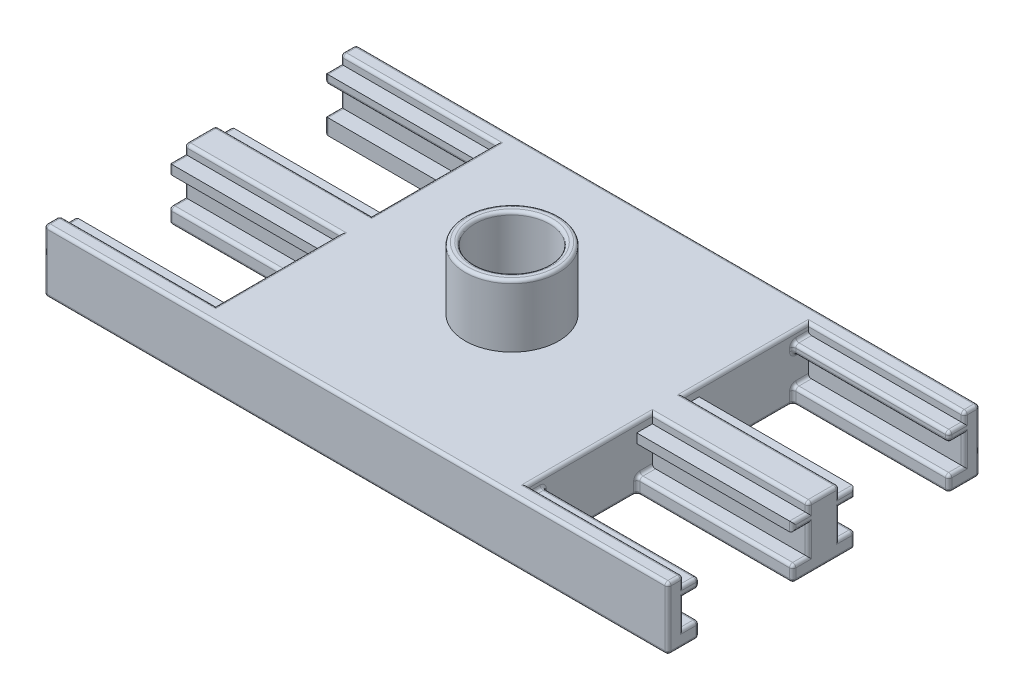
SolidWorks part; units mm, degrees
ref_plane "Front Plane" through (0, 0, 0) normal (0, 0, 1) x (1, 0, 0)
ref_plane "Top Plane" through (0, 0, 0) normal (0, 1, 0) x (1, 0, 0)
ref_plane "Right Plane" through (0, 0, 0) normal (1, 0, 0) x (0, 0, -1)
sketch "Sketch1" plane through (0, 0, 0) normal (0, 1, 0) x (1, 0, 0)
  line L1 (500, -500) -> (-500, -500)
  line L2 (500, -500) -> (500, 500)
  line L3 (500, 500) -> (-500, 500)
  line L4 (-500, -500) -> (-500, 500)
  line L5 (500, -500) -> (-500, 500) construction
  line L6 (500, 500) -> (-500, -500) construction
  point P0 (0, 0)
extrude "Boss-Extrude1" add sketch "Sketch1" along normal blind 200
sketch "Sketch2" plane through (500, 0, 0) normal (1, 0, 0) x (0, 0, -1)
  line L0 (-500, 0) -> (-500, 200)
  line L1 (-500, 200) -> (-500, 0) construction
  line L2 (-500, 200) -> (-450, 200)
  line L4 (-450, 50) -> (-400, 50)
  line L5 (-400, 50) -> (-400, 0)
  line L6 (-500, 0) -> (500, 0) construction
  line L7 (-400, 0) -> (-500, 0)
  line L8 (0, -1000) -> (0, 49000) construction
  line L15 (0, 0) -> (100, 0)
  line L16 (100, 0) -> (100, 50)
  line L17 (100, 50) -> (50, 50)
  line L19 (50, 200) -> (-50, 200)
  line L21 (-50, 50) -> (-100, 50)
  line L22 (-100, 50) -> (-100, 0)
  line L23 (-100, 0) -> (100, 0)
  line L24 (-450, 200) -> (-450, 170)
  line L25 (-450, 170) -> (-400, 170)
  line L26 (-400, 170) -> (-400, 140)
  line L27 (-400, 140) -> (-450, 140)
  line L28 (-450, 140) -> (-450, 50)
  line L29 (450, 140) -> (450, 50)
  line L30 (400, 140) -> (450, 140)
  line L31 (400, 170) -> (400, 140)
  line L32 (450, 170) -> (400, 170)
  line L33 (450, 200) -> (450, 170)
  line L34 (400, 0) -> (500, 0)
  line L35 (400, 50) -> (400, 0)
  line L36 (450, 50) -> (400, 50)
  line L37 (500, 200) -> (450, 200)
  line L38 (500, 0) -> (500, 200)
  line L39 (-50, 200) -> (-50, 170)
  line L40 (-50, 170) -> (-100, 170)
  line L41 (-100, 170) -> (-100, 140)
  line L42 (-100, 140) -> (-50, 140)
  line L43 (-50, 140) -> (-50, 50)
  line L44 (50, 140) -> (50, 50)
  line L45 (100, 140) -> (50, 140)
  line L46 (100, 170) -> (100, 140)
  line L47 (50, 170) -> (100, 170)
  line L48 (50, 200) -> (50, 170)
  point P14 (0, 0)
  point P46 (0, 200)
  dimension "D1" = 30
  dimension "D2" = 30
  dimension "D3" = 50
  dimension "D4" = 90
extrude "Boss-Extrude2" add sketch "Sketch2" along normal blind 500
mirror "Mirror9" about plane through (0, 0, 0) normal (1, 0, 0) of "Boss-Extrude2"
fillet "Fillet1" radius 10 127 edges at (-500, 50, 425) (-500, 25, 400) (-750, 50, 400) (-1000, 0, 450) (-750, 0, 400) (-1000, 100, 500) (-1000, 200, 475) (-750, 200, 450) (-1000, 95, 450) (-1000, 50, 425) (-1000, 25, 400) (-1000, 185, 450) (-1000, 170, 425) (-1000, 155, 400) (-1000, 140, 425) (0, 200, -500) (500, 0, 250) (-500, 0, 250) (-500, 200, 250) (500, 200, 250) (-1000, 200, 0) (-750, 200, 50) (-750, 200, -50) (-1000, 50, -75) (-1000, 25, -100) (-750, 50, -100) (-1000, 0, 0) (-750, 0, -100) (-1000, 25, 100) (-750, 0, 100) (-1000, 50, 75) (-750, 50, 100) (-1000, 95, 50) (-1000, 140, 75) (-1000, 155, 100) (-1000, 170, 75) (-1000, 185, 50) (-1000, 185, -50) (-1000, 170, -75) (-1000, 155, -100) (-1000, 140, -75) (-1000, 95, -50) (-500, 50, 75) (-500, 25, 100) (-500, 25, -100) (-500, 50, -75) (1000, 95, 450) (1000, 140, 425) (1000, 155, 400) (1000, 170, 425) (-500, 0, -250) (-500, 200, -250) (-1000, 95, -450) (1000, 185, 450) (-1000, 140, -425) (-1000, 155, -400) (-750, 140, -400) (-1000, 170, -425) (-1000, 185, -450) (-1000, 200, -475) (-750, 200, -450) (-1000, 100, -500) (-1000, 0, -450) (-1000, 25, -400) (-1000, 50, -425) (-500, 140, -425) (750, 200, 450) (1000, 25, 400) (750, 0, 400) (1000, 50, 425) (750, 50, 400) (1000, 200, 475) (1000, 100, 500) (1000, 0, 450) (500, 50, 425) (500, 25, 400) (500, 170, 425) (500, 155, 400) (500, 140, 425) (500, 0, -250) (500, 200, -250) (0, 0, -500) (750, 200, -50) (750, 200, 50) (500, 50, 75) (500, 25, 100) (750, 50, 100) (750, 0, 100) (500, 25, -100) (750, 0, -100) (500, 50, -75) (750, 50, -100) (1000, 95, -50) (1000, 140, -75) (1000, 155, -100) (1000, 170, -75) (1000, 185, -50) (0, 0, 500) (1000, 200, 0) (1000, 185, 50) (1000, 170, 75) (1000, 155, 100) (1000, 140, 75) (1000, 95, 50) (1000, 50, 75) (1000, 25, 100) (1000, 0, 0) (1000, 25, -100) (1000, 50, -75) (0, 200, 500) (500, 50, -425) (500, 25, -400) (750, 200, -450) (500, 170, -425) (500, 155, -400) (500, 140, -425) (750, 140, -400) (1000, 95, -450) (1000, 50, -425) (1000, 25, -400) (1000, 0, -450) (1000, 100, -500) (1000, 200, -475) (1000, 185, -450) (1000, 170, -425) (1000, 155, -400) (1000, 140, -425)
sketch "Sketch3" plane through (0, 200, 0) normal (0, 1, 0) x (1, 0, 0)
  circle A0 centre (0, 0) radius 150
  circle A1 centre (0, 0) radius 120
extrude "Boss-Extrude3" add sketch "Sketch3" along normal blind 200
fillet "Fillet3" radius 10 2 edges at (0, 400, 120) (0, 400, 150)
